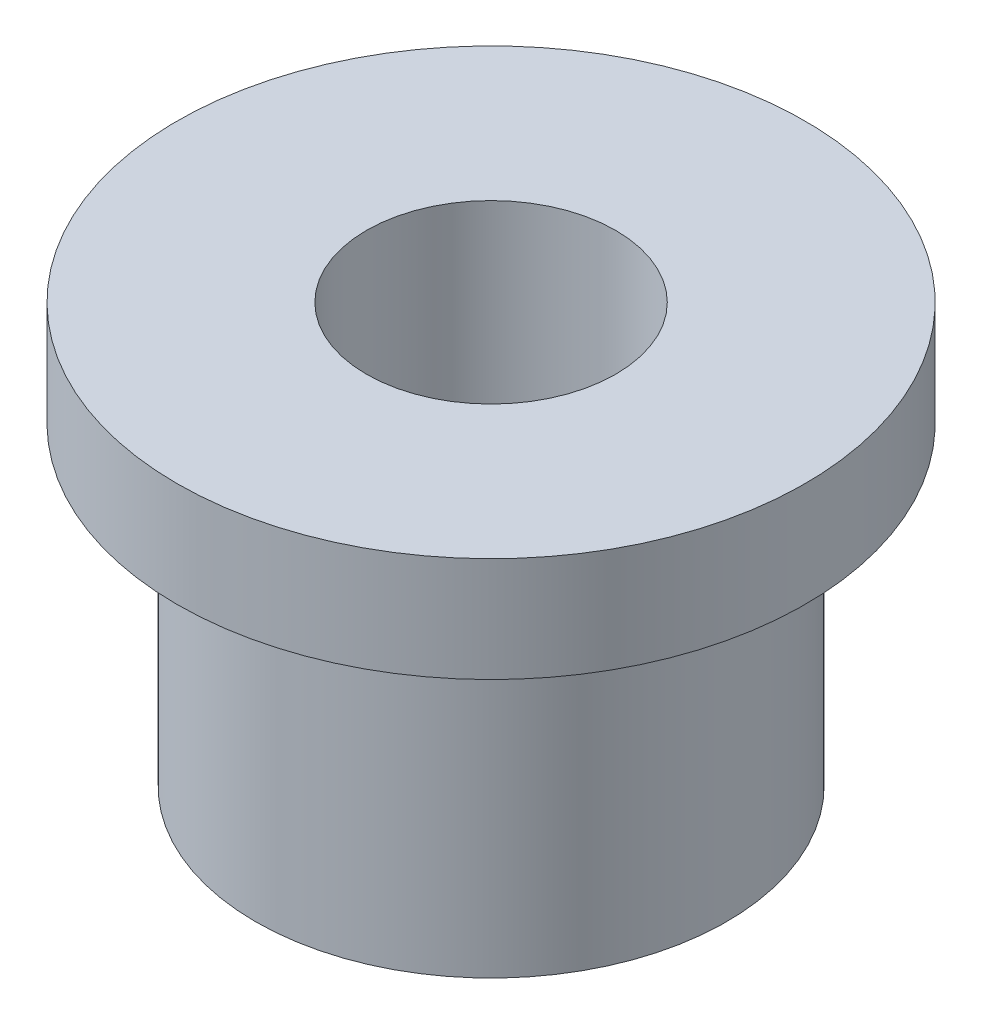
SolidWorks part; units mm, degrees
material "AISI 1020"
ref_plane "Plano frontal" through (0, 0, 0) normal (0, 0, 1) x (1, 0, 0)
ref_plane "Plano superior" through (0, 0, 0) normal (0, 1, 0) x (1, 0, 0)
ref_plane "Plano direito" through (0, 0, 0) normal (1, 0, 0) x (0, 0, -1)
sketch "Esboço1" plane through (0, 0, 0) normal (0, 0, 1) x (1, 0, 0)
  line L0 (0, 8) -> (0, -8) construction
  line L1 (4.7625, 8) -> (12, 8)
  line L2 (12, 8) -> (12, 4)
  line L3 (12, 4) -> (9, 4)
  line L4 (9, 4) -> (9, -8)
  line L5 (9, -8) -> (4.7625, -8)
  line L6 (4.7625, -8) -> (4.7625, 8)
  dimension "D1" = 16
  dimension "D2" = 9.525
  dimension "D3" = 24
  dimension "D4" = 12
  dimension "D5" = 18
revolve "Revolução1" add sketch "Esboço1" angle 360 about L0
